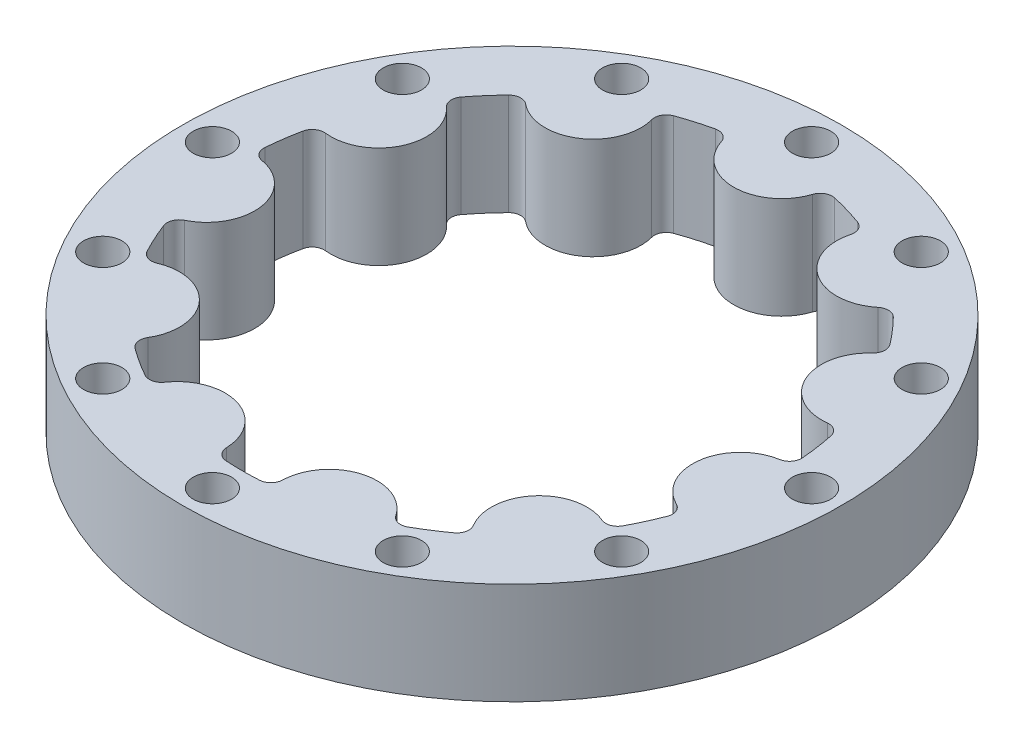
SolidWorks part; units mm, degrees
ref_plane "Front Plane" through (0, 0, 0) normal (0, 0, 1) x (1, 0, 0)
ref_plane "Top Plane" through (0, 0, 0) normal (0, 1, 0) x (1, 0, 0)
ref_plane "Right Plane" through (0, 0, 0) normal (1, 0, 0) x (0, 0, -1)
sketch "Sketch1" plane through (0, 0, 0) normal (0, 1, 0) x (1, 0, 0)
  line L0 (0, 22.5) -> (0, 0) construction
  line L1 (0, 0) -> (12.1644, 18.9282) construction
  line L2 (0, 0) -> (-12.1644, 18.9282) construction
  line L3 (-20.4667, 9.3468) -> (0, 0) construction
  line L4 (0, 0) -> (-22.271, -3.2021) construction
  circle A0 centre (0, 0) radius 22.5
  circle A1 centre (0, 0) radius 27.5
  circle A2 centre (0, 22.5) radius 4
  circle A3 centre (12.1644, 18.9282) radius 4
  circle A4 centre (20.4667, 9.3468) radius 4
  circle A5 centre (22.271, -3.2021) radius 4
  circle A6 centre (17.0044, -14.7344) radius 4
  circle A7 centre (6.339, -21.5886) radius 4
  circle A8 centre (-6.339, -21.5886) radius 4
  circle A9 centre (-17.0044, -14.7344) radius 4
  circle A10 centre (-22.271, -3.2021) radius 4
  circle A11 centre (-20.4667, 9.3468) radius 4
  circle A12 centre (-12.1644, 18.9282) radius 4
  point P27 (0, 0)
  dimension "D1" = 45
  dimension "D2" = 55
  dimension "D3" = 8
  dimension "D4" = 11
extrude "Boss-Extrude2" add sketch "Sketch1" along normal blind 8.5 contours A1 A12 A0 A2 A3 A4 A5 A6 A7 A8 A9 A10 A11 | A0 A11 | A0 A11 | A0 A12 | A0 A12 | A0 A2 | A0 A2 | A0 A3 | A0 A3 | A0 A4 | A0 A4 | A0 A5 | A0 A5 | A0 A6 | A0 A6 | A0 A7 | A0 A7 | A0 A8 | A0 A8 | A0 A9 | A0 A9 | A0 A10 | A0 A10
fillet "Fillet2" radius 1 22 edges at (14.1266, 4.25, 17.5126) (19.3447, 4.25, 11.4905) (2.416, 4.25, 22.3699) (10.0616, 4.25, 20.125) (-10.0616, 4.25, 20.125) (-2.416, 4.25, 22.3699) (-19.3447, 4.25, 11.4905) (-14.1266, 4.25, 17.5126) (-22.4861, 4.25, -0.7921) (-21.352, 4.25, 7.0951) (-18.4882, 4.25, -12.8233) (-21.7984, 4.25, -5.575) (-8.6205, 4.25, -20.7831) (-15.3239, 4.25, -16.4751) (3.9842, 4.25, -22.1444) (-3.9842, 4.25, -22.1444) (15.3239, 4.25, -16.4751) (8.6205, 4.25, -20.7831) (21.7984, 4.25, -5.575) (18.4882, 4.25, -12.8233) (21.352, 4.25, 7.0951) (22.4861, 4.25, -0.7921)
sketch "Sketch2" plane through (0, 0, 0) normal (0, -1, 0) x (1, 0, 0)
  circle A0 centre (0, 0) radius 25 construction
  circle A1 centre (25, 0) radius 1.6
  circle A2 centre (21.6506, -12.5) radius 1.6
  circle A3 centre (12.5, -21.6506) radius 1.6
  circle A4 centre (0, -25) radius 1.6
  circle A5 centre (-12.5, -21.6506) radius 1.6
  circle A6 centre (-21.6506, -12.5) radius 1.6
  circle A7 centre (-25, 0) radius 1.6
  circle A8 centre (-21.6506, 12.5) radius 1.6
  circle A9 centre (-12.5, 21.6506) radius 1.6
  circle A10 centre (0, 25) radius 1.6
  circle A11 centre (12.5, 21.6506) radius 1.6
  circle A12 centre (21.6506, 12.5) radius 1.6
  point P29 (0, 0)
  dimension "D1" = 50
  dimension "D2" = 3.2
  dimension "D3" = 12
extrude "Cut-Extrude1" cut sketch "Sketch2" against normal blind 10
